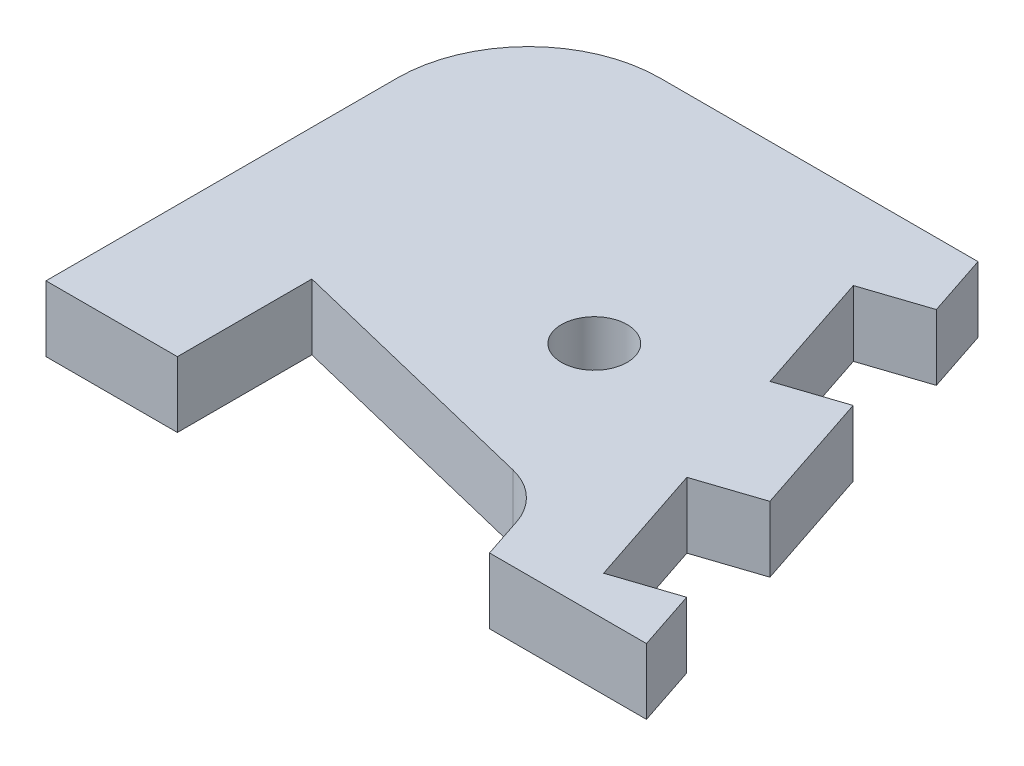
SolidWorks part; units mm, degrees
ref_plane "Front Plane" through (0, 0, 0) normal (0, 0, 1) x (1, 0, 0)
ref_plane "Top Plane" through (0, 0, 0) normal (0, 1, 0) x (1, 0, 0)
ref_plane "Right Plane" through (0, 0, 0) normal (1, 0, 0) x (0, 0, -1)
sketch "Sketch1" plane through (0, 0, 0) normal (0, 1, 0) x (1, 0, 0)
  line L0 (43.536, -35.5951) -> (18.4113, 40)
  line L1 (-50, 40) -> (18.4113, 40)
  line L2 (-50, 40) -> (-50, -13)
  line L3 (-50, -13) -> (-50, -33.4742)
  line L4 (-30, -13) -> (-30, -33.4742)
  line L6 (35, 40) -> (-47.9229, 40) construction
  line L8 (-30, -13) -> (-50, -13) construction
  line L9 (19.645, -35.5951) -> (43.536, -35.5951)
  line L10 (-50, -33.4742) -> (-30, -33.4742)
  line L11 (-30, -13) -> (10.4719, -22.8624)
  line L12 (17.594, -29.4241) -> (19.645, -35.5951)
  line L13 (-30, -26.6965) -> (1.9443, -34.4809) construction
  line L14 (-30, -26.6965) -> (1.9443, -34.4809) construction
  line L15 (45, -40) -> (36.4537, -14.2858) construction
  line L16 (45, -40) -> (36.4537, -14.2858) construction
  circle A0 centre (0, 0) radius 5
  arc A1 (10.4719, -22.8624) -> (17.594, -29.4241) centre (8.1044, -32.578) cw
  dimension "D2" = 10
  dimension "D5" = 10
  dimension "D1" = 50
  dimension "D3" = 53
  dimension "D4" = 20
extrude "Boss-Extrude1" add sketch "Sketch1" along normal blind 10
sketch "Sketch2" plane through (0, 10, 0) normal (0, 1, 0) x (1, 0, 0)
  line L0 (21.5653, 30.5104) -> (12.0757, 27.3564)
  line L1 (43.536, -35.5951) -> (18.4113, 40) construction
  line L2 (12.0757, 27.3564) -> (18.3836, 8.3772)
  line L3 (18.3836, 8.3772) -> (27.8732, 11.5312)
  line L4 (27.8732, 11.5312) -> (34.1811, -7.448) construction
  line L5 (34.1811, -7.448) -> (24.6915, -10.602)
  line L6 (24.6915, -10.602) -> (30.9994, -29.5812)
  line L7 (30.9994, -29.5812) -> (40.489, -26.4272)
  line L8 (21.5653, 30.5104) -> (27.8732, 11.5312)
  line L9 (34.1811, -7.448) -> (40.489, -26.4272)
  dimension "D1" = 20
  dimension "D2" = 20
  dimension "D3" = 20
  dimension "D4" = 10
  dimension "D5" = 10
extrude "Cut-Extrude1" cut sketch "Sketch2" against normal blind 10
fillet "Fillet1" radius 20 1 edges at (-50, 5, -40)
